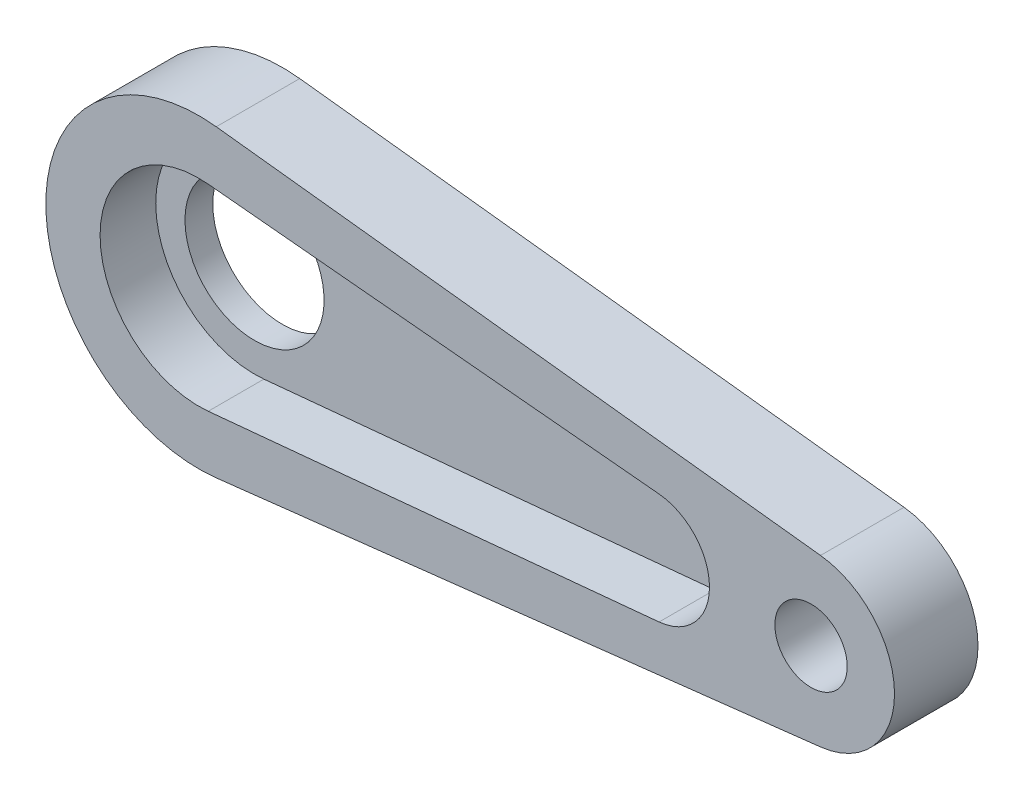
SolidWorks part; units mm, degrees
ref_plane "Front Plane" through (0, 0, 0) normal (0, 0, 1) x (1, 0, 0)
ref_plane "Top Plane" through (0, 0, 0) normal (0, 1, 0) x (1, 0, 0)
ref_plane "Right Plane" through (0, 0, 0) normal (1, 0, 0) x (0, 0, -1)
sketch "Esquisse1" plane through (0, 0, 0) normal (0, 0, 1) x (1, 0, 0)
  line L0 (-3.55, 0) -> (-3.55, 5.3986) construction
  line L1 (0.3365, 3.534) -> (16.5396, 1.991)
  line L2 (16.5396, -1.991) -> (0.3365, -3.534)
  line L3 (18.35, 0) -> (18.35, 4.9554) construction
  line L4 (0.625, 5.4644) -> (22.3409, 2.9806)
  line L5 (0.625, -5.4644) -> (22.3409, -2.9806)
  arc A0 (0.3365, 3.534) -> (0.3365, -3.534) centre (0, 0) ccw
  arc A1 (16.5396, -1.991) -> (16.5396, 1.991) centre (16.35, 0) ccw
  arc A3 (0.625, -5.4644) -> (0.625, 5.4644) centre (0, 0) cw
  arc A4 (22.3409, 2.9806) -> (22.3409, -2.9806) centre (22, 0) cw
  dimension "D2" = 3.55
  dimension "D3" = 2
  dimension "D6" = 5.5
  dimension "D8" = 3
  dimension "D1" = 21.9
  dimension "D7" = 22
extrude "Main" add sketch "Esquisse1" along normal blind 2
sketch "Esquisse2" plane through (0, 0, 0) normal (0, 0, -1) x (-1, 0, 0)
  line L0 (-0.625, -5.4644) -> (-22.3409, -2.9806)
  line L1 (-0.625, -5.4644) -> (-22.3409, -2.9806) construction
  line L3 (-0.625, 5.4644) -> (-22.3409, 2.9806)
  arc A0 (-22.3409, 2.9806) -> (-22.3409, -2.9806) centre (-22, 0) ccw construction
  circle A2 centre (0, 0) radius 2.5
  arc A3 (-0.625, -5.4644) -> (-0.625, 5.4644) centre (0, 0) ccw
  arc A5 (-22.3409, 2.9806) -> (-22.3409, -2.9806) centre (-22, 0) ccw
  dimension "D1" = 5
extrude "OriginalBracket" add sketch "Esquisse2" along normal blind 1
sketch "Esquisse3" plane through (0, 0, 2) normal (0, 0, 1) x (1, 0, 0)
  circle A0 centre (22, 0) radius 1.3
  arc A2 (22.3409, -2.9806) -> (22.3409, 2.9806) centre (22, 0) ccw construction
  point P2 (0, 0)
  dimension "D1" = 2.6
extrude "FixingHole" cut sketch "Esquisse3" against normal through all
